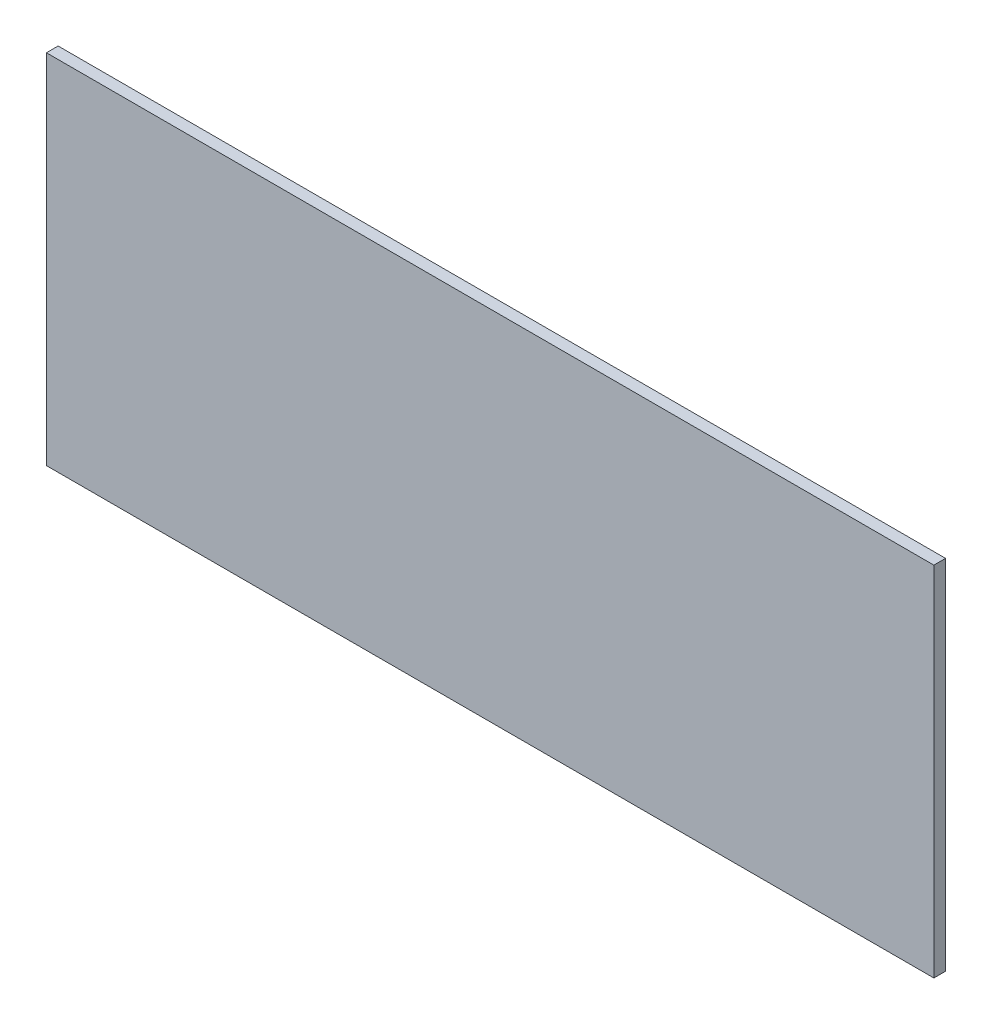
SolidWorks part; units mm, degrees
ref_plane "Front Plane" through (0, 0, 0) normal (0, 0, 1) x (1, 0, 0)
ref_plane "Top Plane" through (0, 0, 0) normal (0, 1, 0) x (1, 0, 0)
ref_plane "Right Plane" through (0, 0, 0) normal (1, 0, 0) x (0, 0, -1)
sketch "Sketch1" plane through (0, 0, 0) normal (0, 0, 1) x (1, 0, 0)
  line L1 (682.5, -275) -> (-682.5, -275)
  line L2 (682.5, -275) -> (682.5, 275)
  line L3 (682.5, 275) -> (-682.5, 275)
  line L4 (-682.5, -275) -> (-682.5, 275)
  line L5 (682.5, -275) -> (-682.5, 275) construction
  line L6 (682.5, 275) -> (-682.5, -275) construction
  point P0 (0, 0)
  dimension "D1" = 550
  dimension "D2" = 1365
extrude "Boss-Extrude1" add sketch "Sketch1" along normal blind 18
equation "\"H_DSP\"=18"
equation "\"D1@Boss-Extrude1\"=\"H_DSP\""
